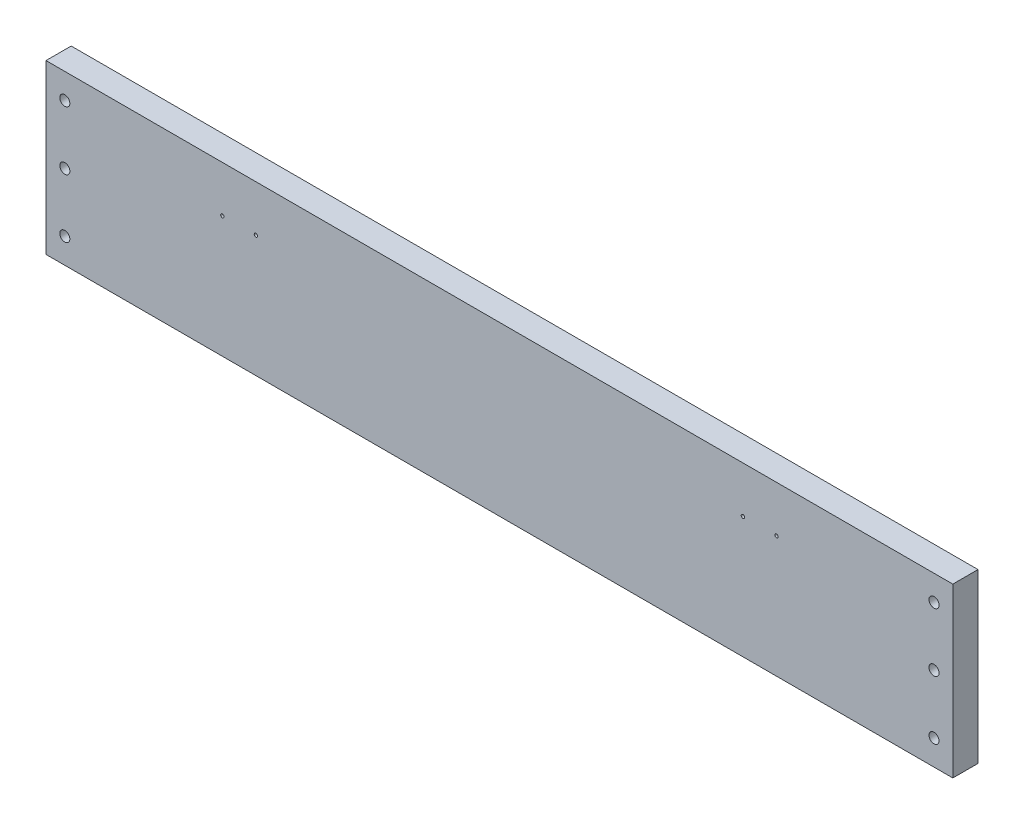
SolidWorks part; units mm, degrees
ref_plane "Front Plane" through (0, 0, 0) normal (0, 0, 1) x (1, 0, 0)
ref_plane "Top Plane" through (0, 0, 0) normal (0, 1, 0) x (1, 0, 0)
ref_plane "Right Plane" through (0, 0, 0) normal (1, 0, 0) x (0, 0, -1)
sketch "Sketch3" plane through (0, 0, 0) normal (0, 1, 0) x (1, 0, 0)
  line L0 (0, 0) -> (685.8, 0)
  line L1 (685.8, 0) -> (685.8, 19.05)
  line L2 (685.8, 19.05) -> (0, 19.05)
  line L3 (0, 0) -> (0, 19.05)
  line L4 (19.05, 19.05) -> (19.05, 0)
  line L5 (666.75, 19.05) -> (666.75, 0)
  dimension "D1" = 685.8
  dimension "D2" = 19.05
  dimension "D3" = 19.05
  dimension "D4" = 19.05
extrude "Boss-Extrude1" add sketch "Sketch3" along normal blind 127 contours L5 L2 L4 L0 | L4 L2 L3 L0 | L2 L5 L0 L1
sketch "Sketch4" plane through (0, 0, 0) normal (0, 0, 1) x (1, 0, 0)
  line L0 (342.9, 0) -> (342.9, 127)
  line L1 (0, 0) -> (685.8, 0) construction
  line L2 (0, 127) -> (685.8, 127) construction
  line L4 (0, 127) -> (0, 0) construction
  circle A0 centre (14.224, 107.95) radius 3.81
  circle A1 centre (14.224, 63.5) radius 3.81
  circle A2 centre (14.224, 19.05) radius 3.81
  circle A3 centre (671.576, 19.05) radius 3.81
  circle A4 centre (671.576, 107.95) radius 3.81
  circle A5 centre (671.576, 63.5) radius 3.81
  dimension "D1" = 7.62
  dimension "D2" = 7.62
  dimension "D3" = 7.62
  dimension "D7" = 14.224
  dimension "D9" = 14.224
  dimension "D8" = 14.224
  dimension "D4" = 44.45
  dimension "D5" = 19.05
  dimension "D6" = 44.45
extrude "Cut-Extrude1" cut sketch "Sketch4" against normal blind 19.05 contours A4 | A5 | A3 | A1 | A0 | A2
sketch "Sketch5" plane through (0, 0, 0) normal (0, 0, 1) x (1, 0, 0)
  line L1 (0, 127) -> (685.8, 127) construction
  line L2 (342.9, 127) -> (342.9, 0)
  line L3 (0, 0) -> (685.8, 0) construction
  line L4 (0, 127) -> (0, 0) construction
  circle A0 centre (133.35, 91.948) radius 1.27
  circle A1 centre (158.75, 91.948) radius 1.27
  circle A2 centre (527.05, 91.948) radius 1.27
  circle A3 centre (552.45, 91.948) radius 1.27
  dimension "D1" = 133.35
  dimension "D2" = 158.75
  dimension "D3" = 2.54
  dimension "D4" = 2.54
  dimension "D5" = 35.052
  dimension "D6" = 35.052
extrude "Cut-Extrude2" cut sketch "Sketch5" against normal blind 114.3 contours A0 | A1 | A2 | A3
